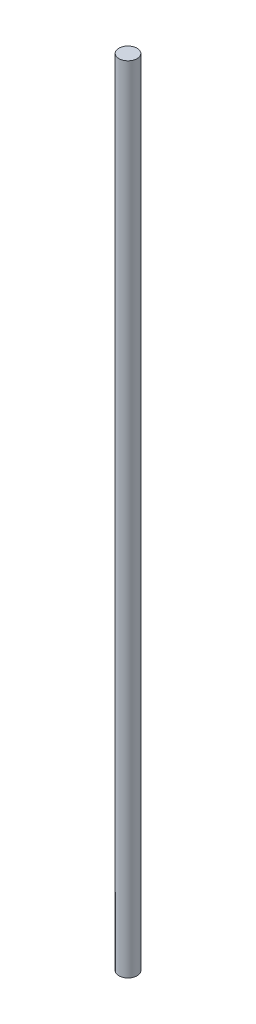
SolidWorks part; units mm, degrees
ref_plane "Front Plane" through (0, 0, 0) normal (0, 0, 1) x (1, 0, 0)
ref_plane "Top Plane" through (0, 0, 0) normal (0, 1, 0) x (1, 0, 0)
ref_plane "Right Plane" through (0, 0, 0) normal (1, 0, 0) x (0, 0, -1)
sketch "Sketch1" plane through (0, 0, 0) normal (0, 1, 0) x (1, 0, 0)
  circle A0 centre (0, 0) radius 4
  dimension "D1" = 8
extrude "Boss-Extrude1" add sketch "Sketch1" along normal blind 350
